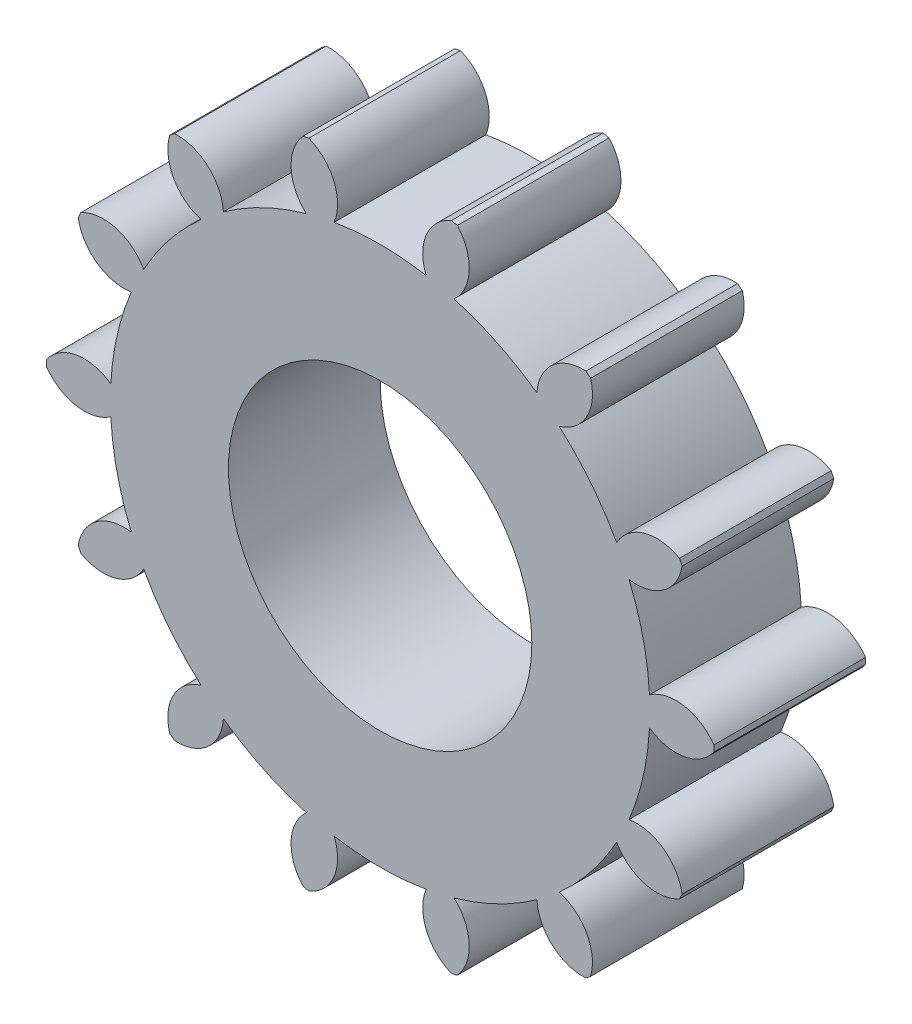
SolidWorks part; units mm, degrees
ref_plane "Front Plane" through (0, 0, 0) normal (0, 0, 1) x (1, 0, 0)
ref_plane "Top Plane" through (0, 0, 0) normal (0, 1, 0) x (1, 0, 0)
ref_plane "Right Plane" through (0, 0, 0) normal (1, 0, 0) x (0, 0, -1)
sketch "Sketch1" plane through (0, 0, 0) normal (0, 0, 1) x (1, 0, 0)
  circle A0 centre (0, 0) radius 6
  circle A1 centre (0, 0) radius 13.2
extrude "Boss-Extrude1" add sketch "Sketch1" along normal blind 6
sketch "Sketch2" plane through (0, 0, 6) normal (0, 0, 1) x (1, 0, 0)
  line L0 (0, 0) -> (0, 15.2) construction
  line L1 (-1.8199, 15.2) -> (0, 0) construction
  line L2 (1.8199, 15.2) -> (0, 0) construction
  arc A0 (-1.8199, 12) -> (1.8199, 12) centre (0, 0) cw
  arc A1 (-2.8199, 12.8953) -> (2.8199, 12.8953) centre (0, 0) cw
  arc A2 (-1.8199, 10.512) -> (1.8199, 10.512) centre (0, 0) cw
  arc A3 (-2.8199, 12.8953) -> (-1.8199, 10.512) centre (-3.5115, 11.2036) cw
  arc A4 (2.8199, 12.8953) -> (1.8199, 10.512) centre (3.5115, 11.2036) ccw
extrude "Cut-Extrude1" cut sketch "Sketch2" against normal through all contours A1 A4 A2 A3
pattern_circular "CirPattern2" count 14 over 360 about axis through (0, 0, 0) along (0, 0, 1) of "Cut-Extrude1"
